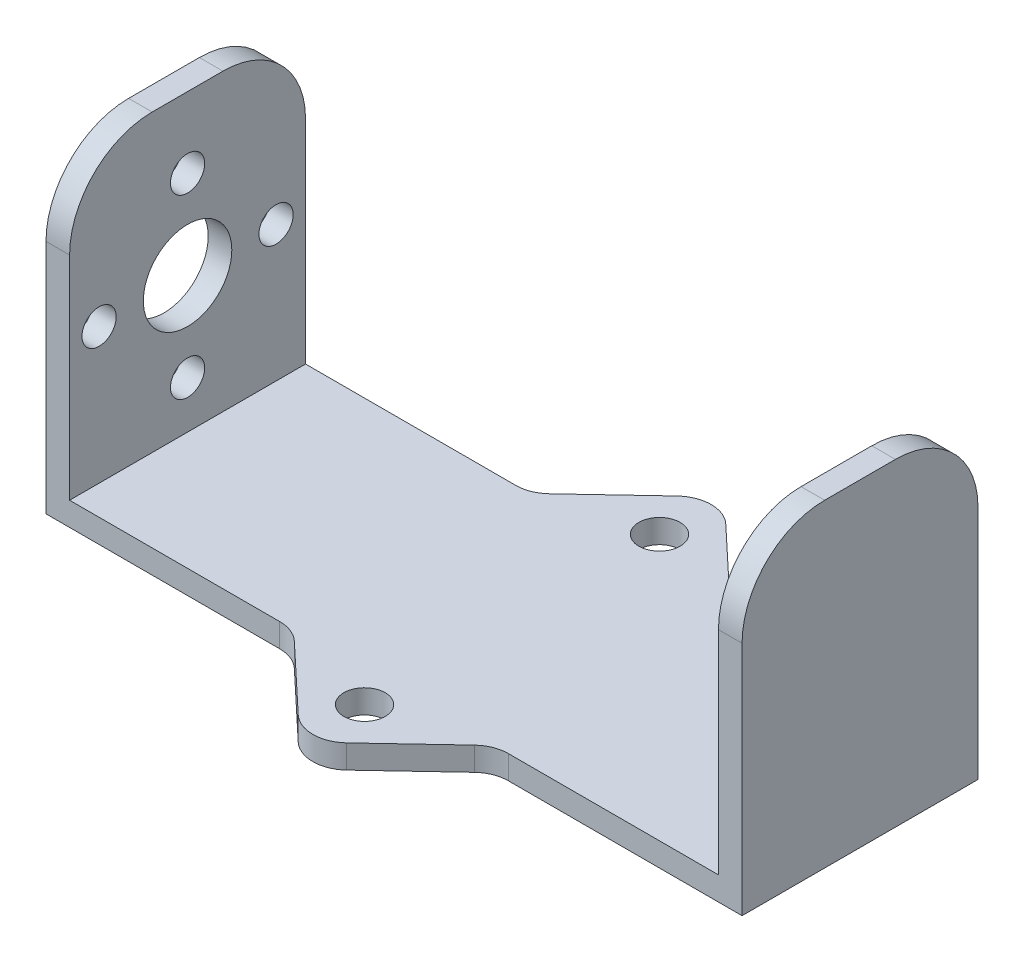
SolidWorks part; units mm, degrees
ref_plane "Front Plane" through (0, 0, 0) normal (0, 0, 1) x (1, 0, 0)
ref_plane "Top Plane" through (0, 0, 0) normal (0, 1, 0) x (1, 0, 0)
ref_plane "Right Plane" through (0, 0, 0) normal (1, 0, 0) x (0, 0, -1)
sketch "Sketch1" plane through (0, 0, 0) normal (0, 0, 1) x (1, 0, 0)
  line L0 (-27.5, 25) -> (-27.5, 0)
  line L1 (-27.5, 0) -> (27.5, 0)
  line L2 (0, 0) -> (0, -2) construction
  line L3 (29.5, -2) -> (-29.5, -2)
  line L4 (-29.5, -2) -> (-29.5, 25)
  line L5 (-29.5, 25) -> (-27.5, 25)
  line L6 (29.5, -2) -> (29.5, 25)
  line L7 (29.5, 25) -> (27.5, 25)
  line L8 (27.5, 25) -> (27.5, 0)
  point P2 (0, 0)
  point P3 (0, -2)
  dimension "D1" = 55
  dimension "D2" = 27
  dimension "D3" = 2
extrude "Boss-Extrude1" add sketch "Sketch1" along normal mid plane 20
fillet "Fillet1" radius 7 4 edges at (-28.5, 25, -10) (-28.5, 25, 10) (28.5, 25, -10) (28.5, 25, 10)
fillet "Fillet2" [suppressed] radius 3
sketch "Sketch2" plane through (-27.5, 0, 0) normal (1, 0, 0) x (0, 0, -1)
  line L1 (-10, 11.5) -> (10, 11.5) construction
  line L2 (-10, 0) -> (-10, 18) construction
  line L3 (10, 0) -> (10, 18) construction
  line L4 (-10, 0) -> (10, 0) construction
  circle A0 centre (0, 11.5) radius 7.5 construction
  circle A1 centre (0, 19) radius 1.45
  circle A2 centre (7.5, 11.5) radius 1.45
  circle A3 centre (0, 4) radius 1.45
  circle A4 centre (-7.5, 11.5) radius 1.45
  circle A5 centre (0, 11.5) radius 3.75
  point P10 (0, 11.5)
  dimension "D1" = 15
  dimension "D2" = 2.9
  dimension "D4" = 7.5
  dimension "D3" = 11.5
extrude "Cut-Extrude1" cut sketch "Sketch2" against normal mid plane 30
sketch "Sketch3" plane through (0, 0, 0) normal (0, 1, 0) x (1, 0, 0)
  line L0 (-8.5, 10) -> (0, 18)
  line L1 (27.5, 10) -> (-27.5, 10) construction
  line L2 (0, 18) -> (8.5, 10)
  line L3 (8.5, 10) -> (-8.5, 10)
  line L4 (0, 0) -> (7.5276, 0) construction
  line L5 (8.5, -10) -> (-8.5, -10)
  line L6 (0, -18) -> (8.5, -10)
  line L7 (-8.5, -10) -> (0, -18)
  dimension "D1" = 8
  dimension "D2" = 17
extrude "Boss-Extrude2" add sketch "Sketch3" against normal up to surface (2 mm away) up to face at (0, -2, 0)
fillet "Fillet3" radius 3 6 edges at (8.5, -1, 10) (0, -1, 18) (-8.5, -1, 10) (0, -1, -18) (8.5, -1, -10) (-8.5, -1, -10)
sketch "Sketch4" plane through (0, 0, 0) normal (0, 1, 0) x (1, 0, 0)
  line L0 (0, -12.5) -> (0, 12.5) construction
  circle A0 centre (0, 12.5) radius 1.75
  circle A1 centre (0, -12.5) radius 1.75
  point P4 (0, 0)
  dimension "D1" = 3.5
  dimension "D2" = 25
extrude "Cut-Extrude2" cut sketch "Sketch4" against normal through all
